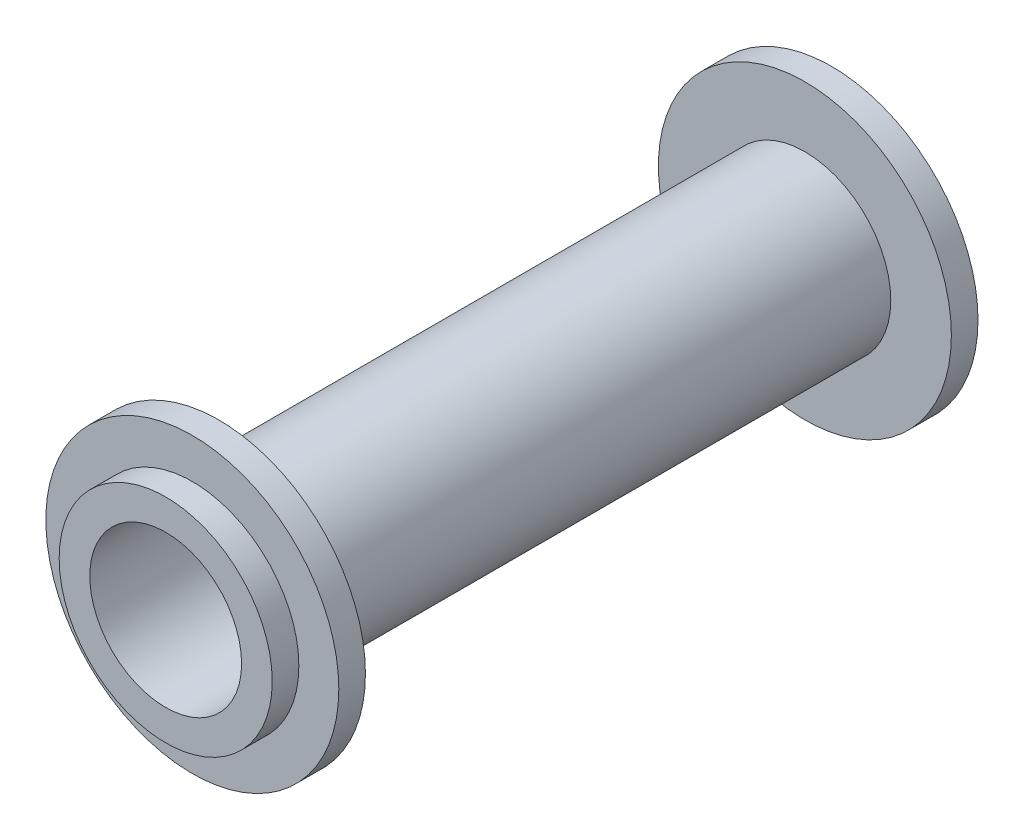
SolidWorks part; units mm, degrees
ref_plane "Front Plane" through (0, 0, 0) normal (0, 0, 1) x (1, 0, 0)
ref_plane "Top Plane" through (0, 0, 0) normal (0, 1, 0) x (1, 0, 0)
ref_plane "Right Plane" through (0, 0, 0) normal (1, 0, 0) x (0, 0, -1)
sketch "Sketch1" plane through (0, 0, 0) normal (0, 0, 1) x (1, 0, 0)
  circle A0 centre (0, 0) radius 8
  dimension "D1" = 16
extrude "Boss-Extrude1" add sketch "Sketch1" along normal blind 2
sketch "Sketch2" plane through (0, 0, 2) normal (0, 0, 1) x (1, 0, 0)
  circle A0 centre (0, 0) radius 11
  dimension "D1" = 22
extrude "Boss-Extrude2" add sketch "Sketch2" along normal blind 2
sketch "Sketch3" plane through (0, 0, 4) normal (0, 0, 1) x (1, 0, 0)
  circle A0 centre (0, 0) radius 6.45
  dimension "D1" = 12.9
extrude "Boss-Extrude3" add sketch "Sketch3" along normal blind 44
sketch "Sketch4" plane through (0, 0, 48) normal (0, 0, 1) x (1, 0, 0)
  circle A0 centre (0, 0) radius 11
  dimension "D1" = 22
extrude "Boss-Extrude4" add sketch "Sketch4" along normal blind 2
sketch "Sketch5" plane through (0, 0, 50) normal (0, 0, 1) x (1, 0, 0)
  circle A0 centre (0, 0) radius 8
  dimension "D1" = 16
extrude "Boss-Extrude5" add sketch "Sketch5" along normal blind 2
sketch "Sketch6" plane through (0, 0, 52) normal (0, 0, 1) x (1, 0, 0)
  circle A0 centre (0, 0) radius 5.7
  dimension "D1" = 11.4
extrude "Cut-Extrude1" cut sketch "Sketch6" against normal through all
